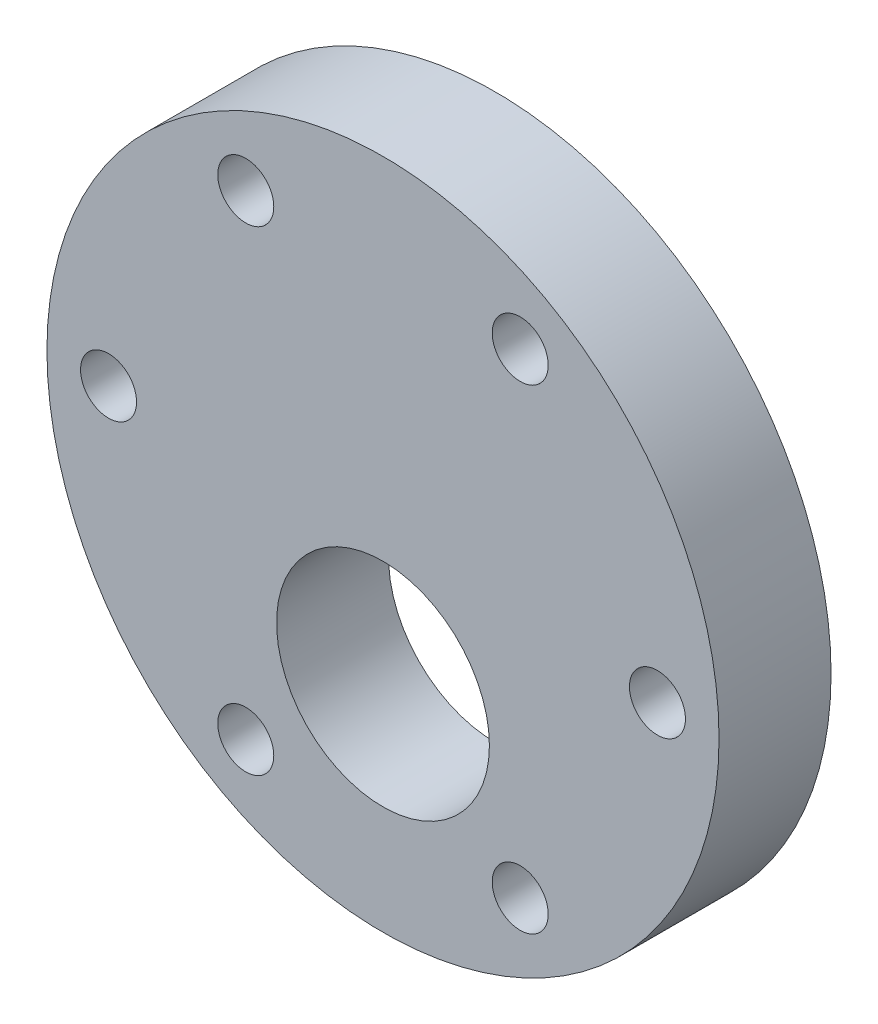
SolidWorks part; units mm, degrees
ref_plane "Front Plane" through (0, 0, 0) normal (0, 0, 1) x (1, 0, 0)
ref_plane "Top Plane" through (0, 0, 0) normal (0, 1, 0) x (1, 0, 0)
ref_plane "Right Plane" through (0, 0, 0) normal (1, 0, 0) x (0, 0, -1)
sketch "Sketch1" plane through (0, 0, 0) normal (0, 0, 1) x (1, 0, 0)
  line L0 (0, 0) -> (0, 19.05) construction
  line L1 (-7.7787, 13.4732) -> (0, 0) construction
  circle A0 centre (0, 0) radius 19.05
  circle A1 centre (0, -6.858) radius 6.0325
  circle A2 centre (0, 0) radius 15.5575 construction
  circle A3 centre (-7.7787, 13.4732) radius 1.5875
  circle A4 centre (7.7787, 13.4732) radius 1.5875
  circle A5 centre (15.5575, 0) radius 1.5875
  circle A6 centre (7.7787, -13.4732) radius 1.5875
  circle A7 centre (-7.7787, -13.4732) radius 1.5875
  circle A8 centre (-15.5575, 0) radius 1.5875
  point P20 (0, 0)
  dimension "D1" = 38.1
  dimension "D2" = 12.065
  dimension "D3" = 31.115
  dimension "D4" = 3.175
  dimension "D7" = 7.7787
  dimension "D6" = 30
  dimension "D8" = 6.858
  dimension "D5" = 6
extrude "Boss-Extrude1" add sketch "Sketch1" along normal blind 6.35
